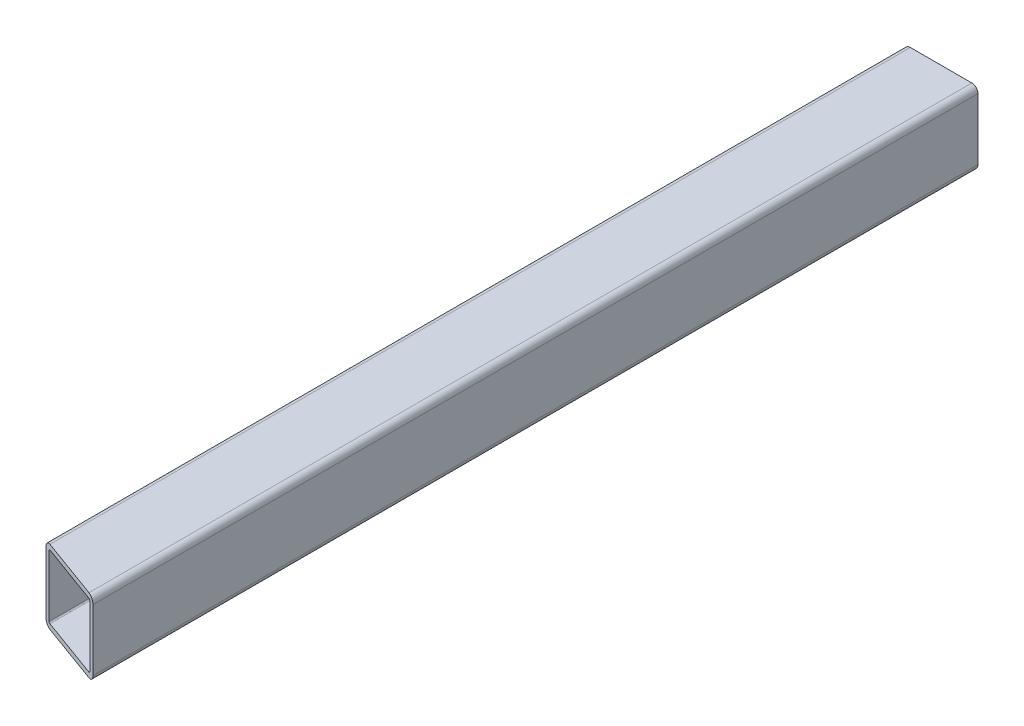
SolidWorks part; units mm, degrees
ref_plane "Front Plane" through (0, 0, 0) normal (0, 0, 1) x (1, 0, 0)
ref_plane "Top Plane" through (0, 0, 0) normal (0, 1, 0) x (1, 0, 0)
ref_plane "Right Plane" through (0, 0, 0) normal (1, 0, 0) x (0, 0, -1)
sketch "Sketch1" plane through (0, 0, 0) normal (0, 0, 1) x (1, 0, 0)
  line L1 (-15.875, 19.05) -> (15.875, 19.05)
  line L2 (-19.05, 15.875) -> (-19.05, -15.875)
  line L3 (-15.875, -19.05) -> (15.875, -19.05)
  line L4 (19.05, 15.875) -> (19.05, -15.875)
  line L5 (-19.05, 19.05) -> (19.05, -19.05) construction
  line L6 (-19.05, -19.05) -> (19.05, 19.05) construction
  arc A0 (-19.05, -15.875) -> (-15.875, -19.05) centre (-15.875, -15.875) ccw
  arc A1 (15.875, -19.05) -> (19.05, -15.875) centre (15.875, -15.875) ccw
  arc A2 (19.05, 15.875) -> (15.875, 19.05) centre (15.875, 15.875) ccw
  arc A3 (-15.875, 19.05) -> (-19.05, 15.875) centre (-15.875, 15.875) ccw
  point P0 (0, 0)
  dimension "D3" = 3.175
  dimension "D1" = 38.1
  dimension "D2" = 38.1
extrude "Extrude-Thin1" add sketch "Sketch1" along normal mid plane 457.2 thin
sketch "Sketch2" plane through (0, 19.05, 0) normal (0, 1, 0) x (1, 0, 0)
  line L0 (0, 228.6) -> (0, -228.6) construction
  line L1 (15.875, 228.6) -> (-15.875, 228.6) construction
  line L2 (15.875, -228.6) -> (-15.875, -228.6) construction
  line L3 (-15.875, 209.55) -> (15.875, 209.55) construction
  line L4 (-15.875, -228.6) -> (-15.875, 228.6) construction
  line L5 (15.875, -228.6) -> (15.875, 228.6) construction
  dimension "D1" = 19.05
sketch "Sketch3" plane through (0, 19.05, 0) normal (0, 1, 0) x (1, 0, 0)
  line L0 (19.05, -228.6) -> (-19.05, -214.7327)
  line L1 (-19.05, -228.6) -> (-19.05, 228.6) construction
  line L2 (15.875, -228.6) -> (-15.875, -228.6) construction
  dimension "D1" = 20
extrude "Cut-Extrude1" cut sketch "Sketch3" against normal through all and the other way through all
sketch "Sketch4" plane through (-19.05, 0, 0) normal (-1, 0, 0) x (0, 0, 1)
  line L0 (-228.6, 0) -> (214.7327, 0) construction
  line L2 (-228.6, 15.875) -> (-228.6, -15.875) construction
  line L4 (214.7327, 15.875) -> (214.7327, -15.875) construction
  line L5 (-209.55, 19.05) -> (-209.55, -15.875) construction
  line L6 (215.8883, 19.05) -> (-228.6, 19.05) construction
  line L7 (214.7327, -15.875) -> (-228.6, -15.875) construction
  line L8 (-133.35, 15.875) -> (-133.35, -15.875) construction
  line L9 (214.7327, 15.875) -> (-228.6, 15.875) construction
  line L10 (-57.15, 15.875) -> (-57.15, -15.875) construction
  line L11 (171.45, 15.875) -> (171.45, -15.875) construction
  line L12 (19.05, 15.875) -> (19.05, -15.875) construction
  line L13 (95.25, 15.875) -> (95.25, -15.875) construction
  dimension "D1" = 19.05
  dimension "D2" = 76.2
  dimension "D3" = 76.2
  dimension "D4" = 76.2
  dimension "D5" = 76.2
  dimension "D6" = 76.2
